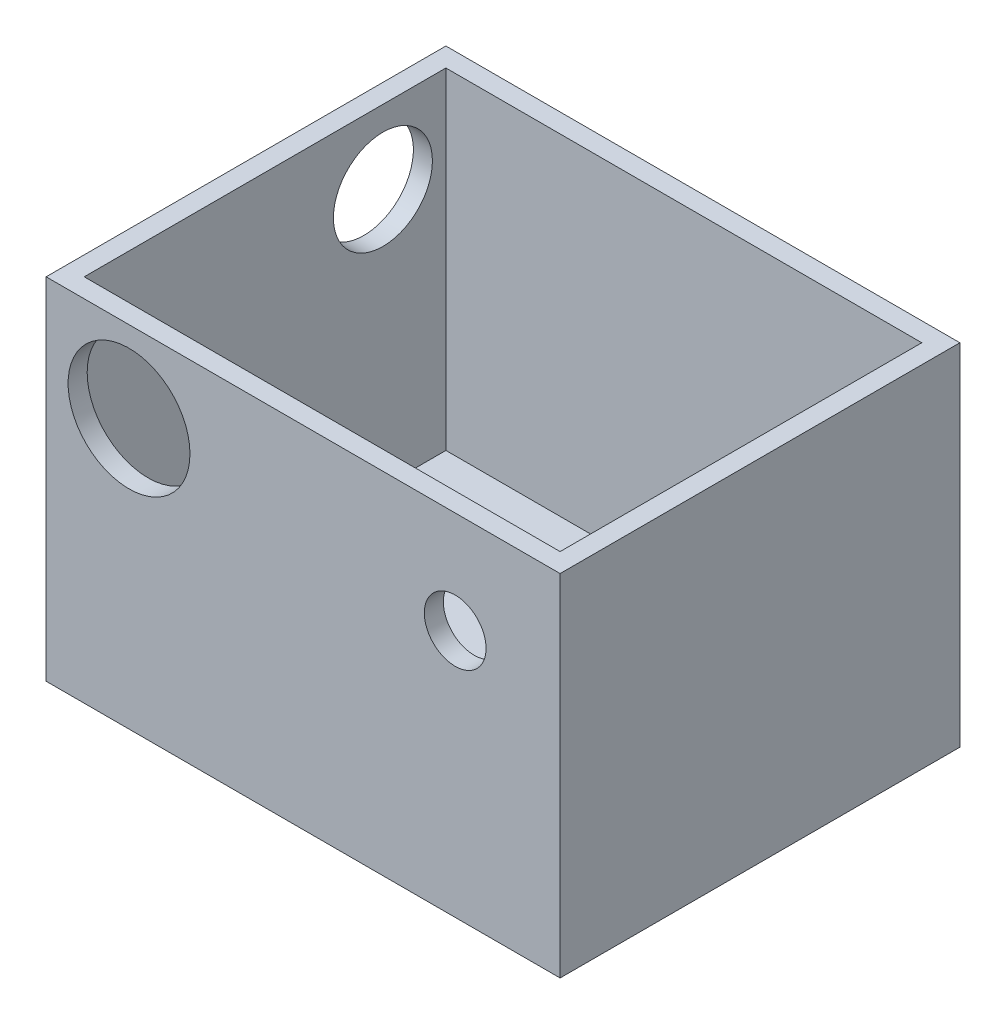
SolidWorks part; units mm, degrees
ref_plane "Front Plane" through (0, 0, 0) normal (0, 0, 1) x (1, 0, 0)
ref_plane "Top Plane" through (0, 0, 0) normal (0, 1, 0) x (1, 0, 0)
ref_plane "Right Plane" through (0, 0, 0) normal (1, 0, 0) x (0, 0, -1)
sketch "Sketch1" plane through (0, 0, 0) normal (0, 1, 0) x (1, 0, 0)
  line L1 (-42.8625, 33.3375) -> (42.8625, 33.3375)
  line L2 (-42.8625, 33.3375) -> (-42.8625, -33.3375)
  line L3 (-42.8625, -33.3375) -> (42.8625, -33.3375)
  line L4 (42.8625, 33.3375) -> (42.8625, -33.3375)
  line L5 (-42.8625, 33.3375) -> (42.8625, -33.3375) construction
  line L6 (-42.8625, -33.3375) -> (42.8625, 33.3375) construction
  line L8 (-42.8625, 16.04) -> (-42.8625, -5.457)
  point P0 (0, 0)
  dimension "D1" = 85.725
  dimension "D2" = 66.675
extrude "Boss-Extrude2" add sketch "Sketch1" along normal blind 58.42 contours L1 L4 L3 L2
shell "Shell1" thickness 3.175
hole_wizard "Hole1" positions "Sketch12" profile "Sketch14" legacy
sketch "Sketch12" plane through (0, 0, 33.3375) normal (0, 0, 1) x (1, 0, 0)
  point P10 (-29.0335, 44.8588)
  point P40 (-29.0335, 44.8588)
sketch "Sketch14" plane through (-29.0335, 44.8588, 33.3375) normal (1, 0, 0) x (0, -1, 0)
  line L0 (0, 0) -> (0, 66.675)
  line L1 (0, 66.675) -> (10.16, 66.675)
  line L2 (10.16, 66.675) -> (10.16, 0)
  line L3 (10.16, 0) -> (0, 0)
  line L4 (0, 110) -> (0, -10) construction
  dimension "Diameter" = 20.32
  dimension "Depth" = 66.675
hole_wizard "Hole2" positions "Sketch18" profile "Sketch19" legacy
sketch "Sketch18" plane through (-42.8625, 0, 0) normal (-1, 0, 0) x (0, 0, 1)
  point P0 (-19.6582, 46.1469)
sketch "Sketch19" plane through (-42.8625, 46.1469, -19.6582) normal (0, 1, 0) x (0, 0, 1)
  line L0 (0, 0) -> (0, 3.175)
  line L1 (0, 3.175) -> (8.255, 3.175)
  line L2 (8.255, 3.175) -> (8.255, 0)
  line L3 (8.255, 0) -> (0, 0)
  line L4 (0, 110) -> (0, -10) construction
  dimension "Diameter" = 16.51
  dimension "Depth" = 3.175
hole_wizard "Hole3" positions "Sketch20" profile "Sketch21" legacy
sketch "Sketch20" plane through (0, 0, 33.3375) normal (0, 0, 1) x (1, 0, 0)
  line L0 (42.8625, 58.42) -> (42.8625, 0) construction
  line L1 (-42.8625, 58.42) -> (42.8625, 58.42) construction
  line L2 (39.6875, 58.42) -> (39.6875, 3.175) construction
  point P0 (25.3625, 41.42)
  dimension "D1" = 17.5
  dimension "D2" = 17
  dimension "D3" = 14.325
sketch "Sketch21" plane through (25.3625, 41.42, 33.3375) normal (1, 0, 0) x (0, -1, 0)
  line L0 (0, 0) -> (0, 3.175)
  line L1 (0, 3.175) -> (5.15, 3.175)
  line L2 (5.15, 3.175) -> (5.15, 0)
  line L3 (5.15, 0) -> (0, 0)
  line L4 (0, 110) -> (0, -10) construction
  dimension "Diameter" = 10.3
  dimension "Depth" = 3.175
equation "\"3.00mmin\"=3"
equation "\"3.00inn\"=3"
equation "\"0.50inn\"=0.1"
